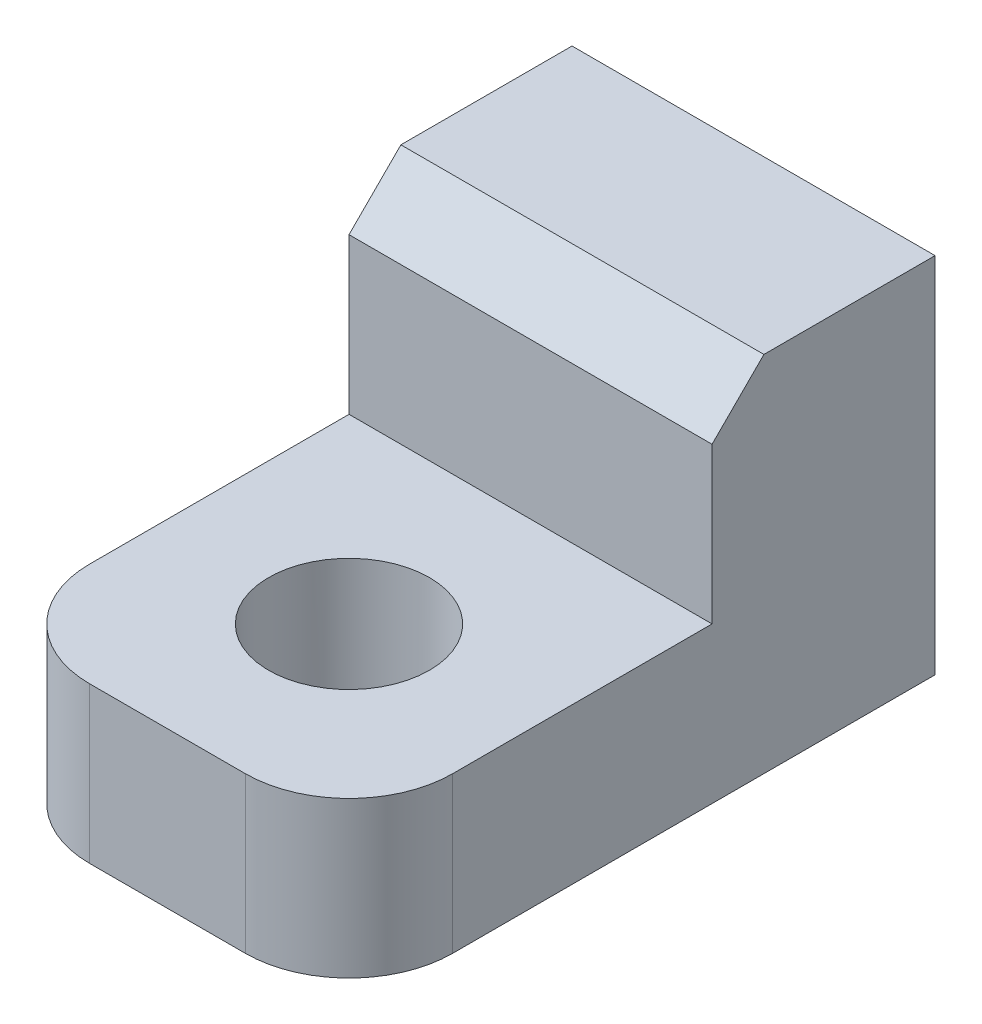
SolidWorks part; units mm, degrees
ref_plane "Front Plane" through (0, 0, 0) normal (0, 0, 1) x (1, 0, 0)
ref_plane "Top Plane" through (0, 0, 0) normal (0, 1, 0) x (1, 0, 0)
ref_plane "Right Plane" through (0, 0, 0) normal (1, 0, 0) x (0, 0, -1)
sketch "Sketch1" plane through (0, 0, 0) normal (0, 0, 1) x (1, 0, 0)
  line L0 (0, 0) -> (0, 136) construction
  line L1 (-48.8, 3) -> (142.2, 3) construction
  line L2 (0, 0) -> (0, 136)
  line L3 (-48.8, 3) -> (142.2, 3)
  line L4 (1.5, 3) -> (1.5, 10)
  line L5 (1.5, 10) -> (8.5, 10)
  line L6 (8.5, 10) -> (8.5, 3)
  circle A0 centre (5, 6.5) radius 1.55 construction
  circle A1 centre (5, 6.5) radius 1.55
  dimension "D1" = 3.5
  dimension "D2" = 3.5
  dimension "D3" = 7
extrude "Boss-Extrude1" add sketch "Sketch1" along normal blind 2.3 contours L6 L5 L4 L3 A1
sketch "Sketch3" plane through (0, 0, 2.3) normal (0, 0, 1) x (1, 0, 0)
  line L0 (1.5, 10) -> (8.5, 10) construction
  line L1 (1.5, 3) -> (1.5, 10) construction
  line L2 (1.5, 3) -> (8.5, 3) construction
  line L3 (8.5, 10) -> (8.5, 3) construction
  line L4 (1.5, 10) -> (8.5, 10)
  line L5 (1.5, 3) -> (1.5, 10)
  line L6 (1.5, 3) -> (8.5, 3)
  line L7 (8.5, 10) -> (8.5, 3)
extrude "Boss-Extrude2" add sketch "Sketch3" along normal blind 2
sketch "Sketch4" plane through (0, 0, 4.3) normal (0, 0, 1) x (1, 0, 0)
  line L0 (8.5, 3) -> (8.5, 10) construction
  line L1 (1.5, 3) -> (8.5, 3)
  line L2 (1.5, 3) -> (1.5, 6)
  line L3 (1.5, 6) -> (8.5, 6)
  line L4 (8.5, 3) -> (8.5, 6)
  dimension "D1" = 3
extrude "Boss-Extrude3" add sketch "Sketch4" along normal blind 7
sketch "Sketch5" plane through (0, 3, 0) normal (0, -1, 0) x (1, 0, 0)
  line L0 (1.5, 11.3) -> (8.5, 11.3) construction
  circle A0 centre (5, 7.8) radius 1.55
  dimension "D1" = 3.1
  dimension "D2" = 3.5
extrude "Cut-Extrude1" cut sketch "Sketch5" against normal up to next
fillet "Fillet1" radius 2 2 edges at (8.5, 4.5, 11.3) (1.5, 4.5, 11.3)
chamfer "Chamfer1" distance 1 angle 45 1 edges at (5, 10, 4.3)
